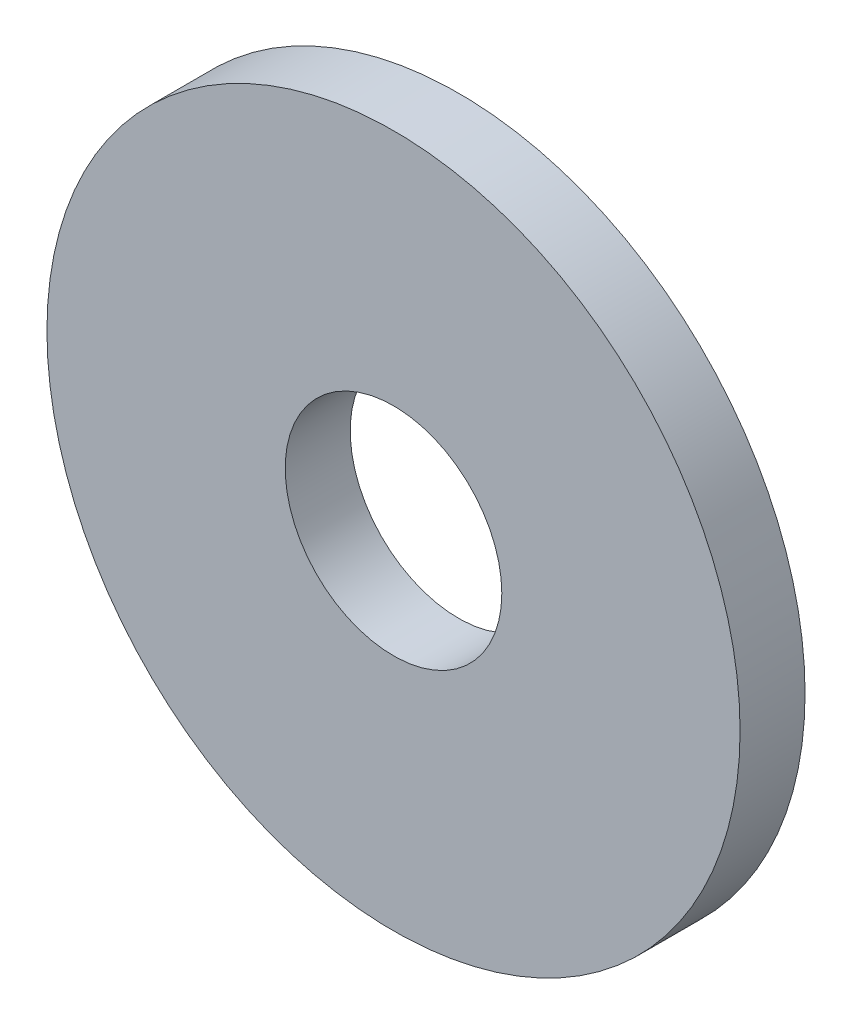
SolidWorks part; units mm, degrees
material "6061-T6 (SS)"
ref_plane "Front Plane" through (0, 0, 0) normal (0, 0, 1) x (1, 0, 0)
ref_plane "Top Plane" through (0, 0, 0) normal (0, 1, 0) x (1, 0, 0)
ref_plane "Right Plane" through (0, 0, 0) normal (1, 0, 0) x (0, 0, -1)
sketch "Sketch1" plane through (0, 0, 0) normal (0, 0, 1) x (1, 0, 0)
  circle A0 centre (0, 0) radius 16
  circle A1 centre (0, 0) radius 5
  dimension "D1" = 32
  dimension "D2" = 10
extrude "Extrude1" add sketch "Sketch1" along normal blind 3
